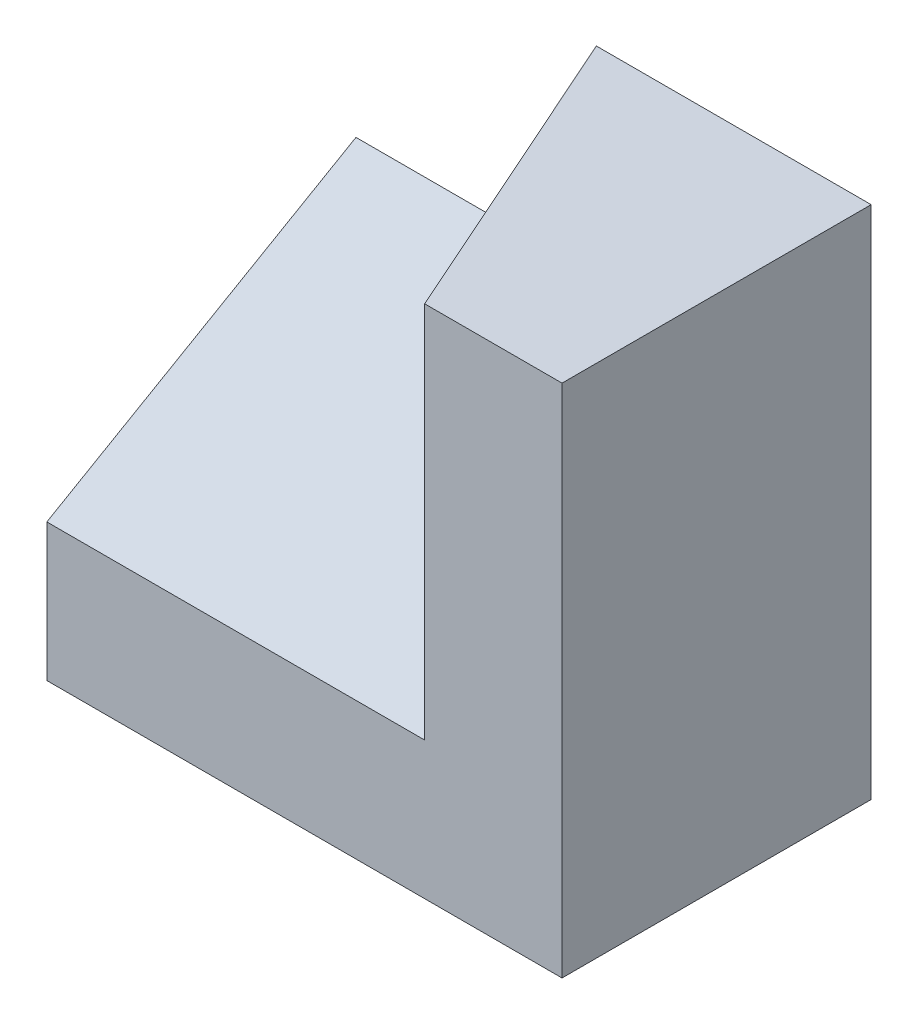
SolidWorks part; units mm, degrees
ref_plane "Front" through (0, 0, 0) normal (0, 0, 1) x (1, 0, 0)
ref_plane "Top" through (0, 0, 0) normal (0, 1, 0) x (1, 0, 0)
ref_plane "Right" through (0, 0, 0) normal (1, 0, 0) x (0, 0, -1)
sketch "Sketch1" plane through (0, 0, 0) normal (0, 1, 0) x (1, 0, 0)
  line L0 (0, 0) -> (0, -45)
  line L1 (0, -45) -> (-20, -45)
  line L2 (-20, -45) -> (-40, 0)
  line L3 (-40, 0) -> (0, 0)
  dimension "D1" = 45
  dimension "D2" = 20
  dimension "D3" = 40
extrude "Extrude1" add sketch "Sketch1" along normal blind 75
sketch "Sketch2" plane through (0, 0, 0) normal (1, 0, 0) x (0, 0, -1)
  line L0 (-45, 20) -> (-45, 0)
  line L1 (-45, 75) -> (-45, 0) construction
  line L2 (-45, 0) -> (0, 0)
  line L3 (0, 0) -> (0, 45.9808)
  line L4 (0, 75) -> (0, 0) construction
  line L5 (0, 45.9808) -> (-45, 20)
  dimension "D1" = 20
  dimension "D2" = 30
extrude "Extrude2" add sketch "Sketch2" against normal blind 75
